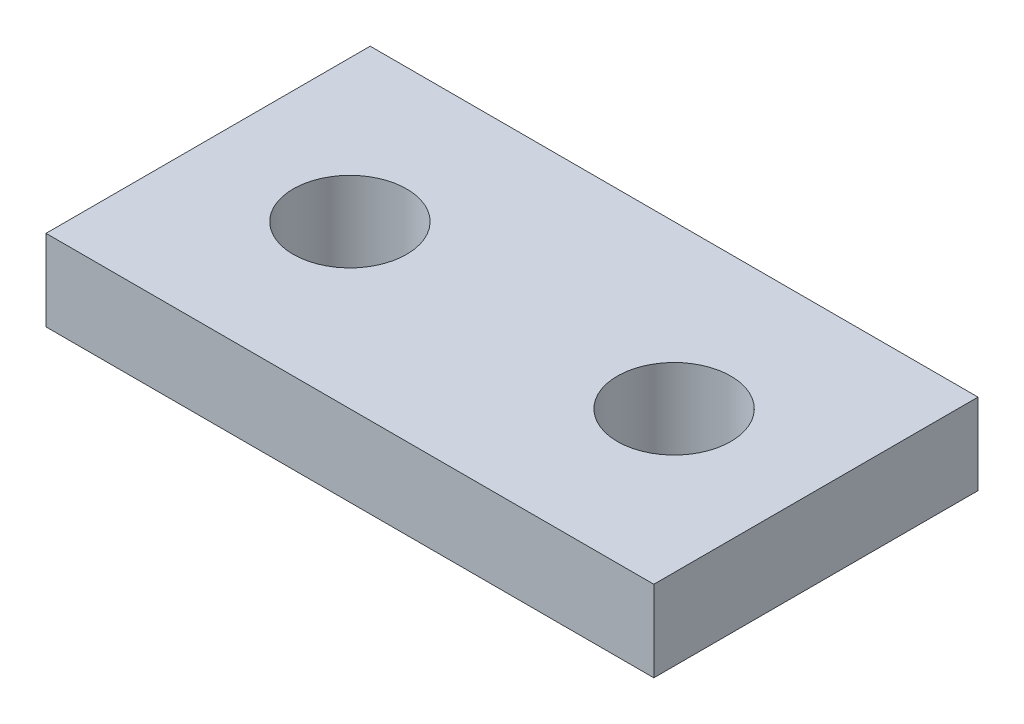
SolidWorks part; units mm, degrees
ref_plane "Front Plane" through (0, 0, 0) normal (0, 0, 1) x (1, 0, 0)
ref_plane "Top Plane" through (0, 0, 0) normal (0, 1, 0) x (1, 0, 0)
ref_plane "Right Plane" through (0, 0, 0) normal (1, 0, 0) x (0, 0, -1)
sketch "Sketch1" plane through (0, 0, 0) normal (0, 1, 0) x (1, 0, 0)
  line L1 (-9.525, 0) -> (9.525, 0)
  line L2 (-9.525, 0) -> (-9.525, 10.16)
  line L3 (-9.525, 10.16) -> (9.525, 10.16)
  line L4 (9.525, 0) -> (9.525, 10.16)
  circle A0 centre (-5.08, 5.08) radius 1.778
  circle A1 centre (5.08, 5.08) radius 1.778
  point P9 (0, 0)
  dimension "D1" = 3.556
  dimension "D2" = 3.556
  dimension "D3" = 10.16
  dimension "D4" = 19.05
  dimension "D5" = 4.445
  dimension "D6" = 10.16
  dimension "D7" = 5.08
extrude "Boss-Extrude1" add sketch "Sketch1" along normal blind 2.54
